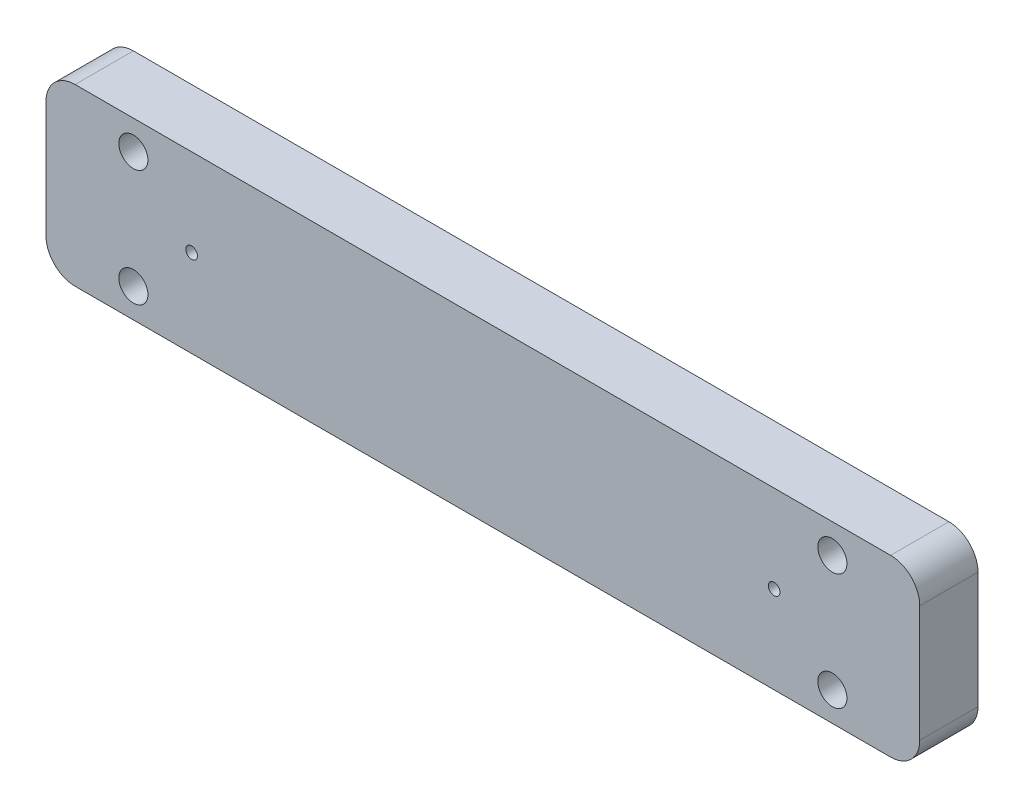
SolidWorks part; units mm, degrees
ref_plane "Front Plane" through (0, 0, 0) normal (0, 0, 1) x (1, 0, 0)
ref_plane "Top Plane" through (0, 0, 0) normal (0, 1, 0) x (1, 0, 0)
ref_plane "Right Plane" through (0, 0, 0) normal (1, 0, 0) x (0, 0, -1)
sketch "Sketch1" plane through (0, 0, 0) normal (0, 0, 1) x (1, 0, 0)
  line L1 (5, 0) -> (145, 0)
  line L2 (0, 5) -> (0, 25)
  line L3 (5, 30) -> (145, 30)
  line L4 (150, 5) -> (150, 25)
  arc A0 (145, 0) -> (150, 5) centre (145, 5) ccw
  arc A1 (145, 30) -> (150, 25) centre (145, 25) cw
  arc A2 (5, 0) -> (0, 5) centre (5, 5) cw
  arc A3 (0, 25) -> (5, 30) centre (5, 25) cw
  circle A6 centre (25, 15) radius 1
  circle A7 centre (125, 15) radius 1
  point P9 (150, 30)
  point P12 (0, 0)
  point P15 (0, 30)
  dimension "D3" = 5
  dimension "D4" = 100
  dimension "D5" = 15
  dimension "D6" = 25
  dimension "D11" = 2
  dimension "D1" = 30
  dimension "D2" = 150
extrude "Boss-Extrude1" add sketch "Sketch1" along normal blind 10
sketch "Sketch2" plane through (0, 0, 10) normal (0, 0, 1) x (1, 0, 0)
  line L0 (5, 0) -> (145, 0) construction
  line L1 (15, 25) -> (135, 25) construction
  line L2 (15, 25) -> (15, 5) construction
  line L3 (15, 5) -> (135, 5) construction
  line L4 (135, 25) -> (135, 5) construction
  circle A0 centre (15, 25) radius 2.5
  circle A1 centre (15, 5) radius 2.5
  circle A2 centre (135, 25) radius 2.5
  circle A3 centre (135, 5) radius 2.5
  circle A4 centre (25, 15) radius 1 construction
  circle A5 centre (125, 15) radius 1 construction
  dimension "D1" = 5
  dimension "D4" = 10
  dimension "D5" = 10
  dimension "D2" = 20
  dimension "D3" = 5
extrude "Cut-Extrude1" cut sketch "Sketch2" against normal through all
